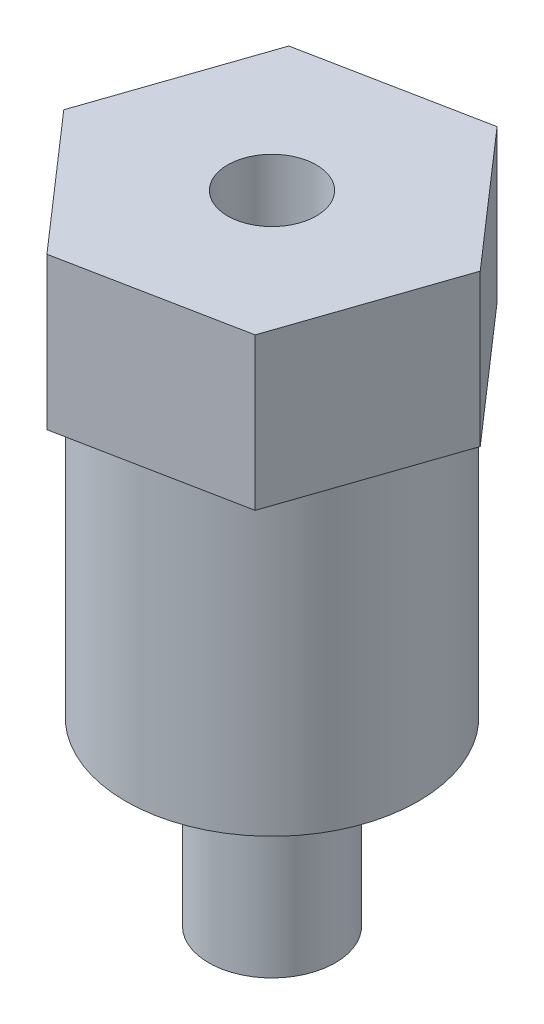
SolidWorks part; units mm, degrees
ref_plane "Front Plane" through (0, 0, 0) normal (0, 0, 1) x (1, 0, 0)
ref_plane "Top Plane" through (0, 0, 0) normal (0, 1, 0) x (1, 0, 0)
ref_plane "Right Plane" through (0, 0, 0) normal (1, 0, 0) x (0, 0, -1)
sketch "Sketch1" plane through (0, 0, 0) normal (0, 1, 0) x (1, 0, 0)
  line L1 (4.6059, -5.2712) -> (6.868, 1.3532)
  line L2 (6.868, 1.3532) -> (2.262, 6.6244)
  line L3 (2.262, 6.6244) -> (-4.6059, 5.2712)
  line L4 (-4.6059, 5.2712) -> (-6.868, -1.3532)
  line L5 (-6.868, -1.3532) -> (-2.262, -6.6244)
  line L6 (-2.262, -6.6244) -> (4.6059, -5.2712)
  circle A0 centre (0, 0) radius 7 construction
  dimension "D1" = 14
extrude "Boss-Extrude1" add sketch "Sketch1" along normal blind 6
sketch "Sketch2" plane through (0, 6, 0) normal (0, 1, 0) x (1, 0, 0)
  circle A0 centre (0, 0) radius 5.775
  dimension "D1" = 11.55
extrude "Boss-Extrude2" add sketch "Sketch2" against normal blind 18
sketch "Sketch3" plane through (0, -12, 0) normal (0, -1, 0) x (1, 0, 0)
  circle A0 centre (0, 0) radius 2.5
  dimension "D1" = 5
extrude "Boss-Extrude3" add sketch "Sketch3" along normal blind 7.16
sketch "Sketch4" plane through (0, 6, 0) normal (0, 1, 0) x (1, 0, 0)
  circle A0 centre (0, 0) radius 1.75
  dimension "D1" = 3.5
extrude "Cut-Extrude1" cut sketch "Sketch4" against normal blind 10
sketch "Sketch5" plane through (-5.7369, 0, -1.959) normal (-0.9463, 0, -0.3231) x (-0.3231, 0, 0.9463)
  line L0 (3.5, 6) -> (3.5, -19.1645)
  dimension "D1" = 25.1645
